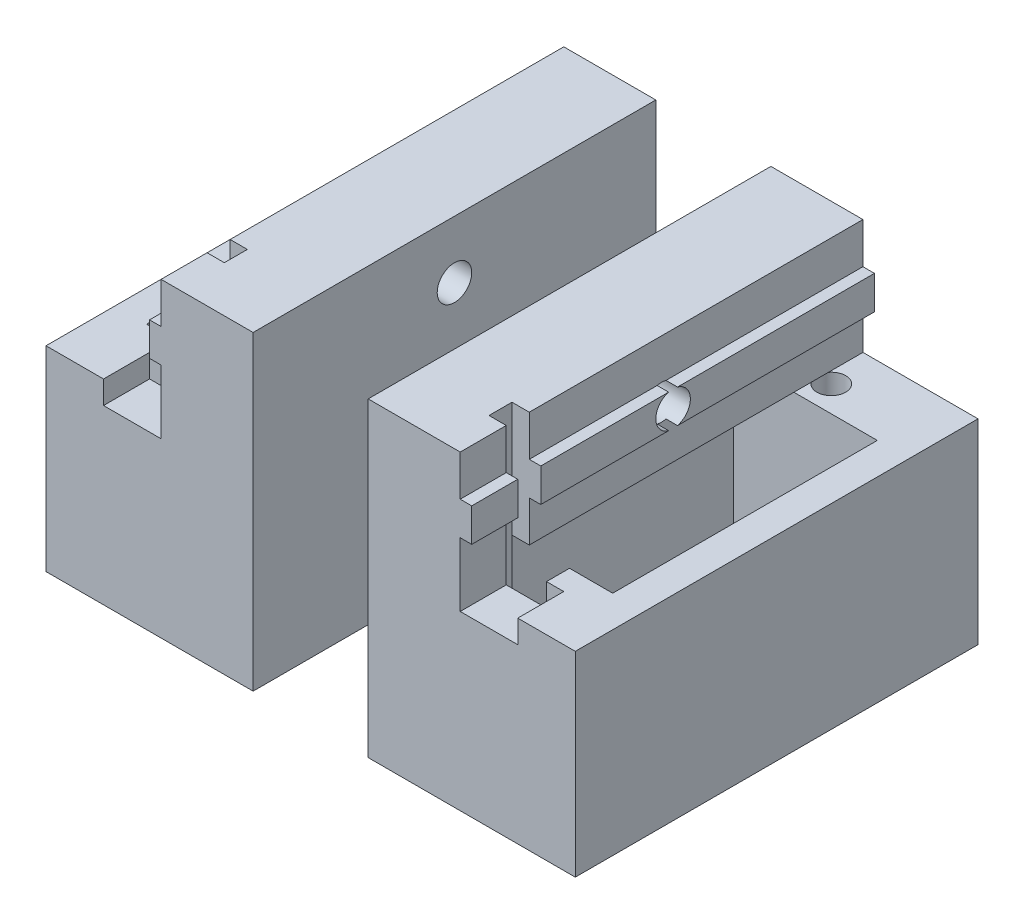
SolidWorks part; units mm, degrees
ref_plane "Front Plane" through (0, 0, 0) normal (0, 0, 1) x (1, 0, 0)
ref_plane "Top Plane" through (0, 0, 0) normal (0, 1, 0) x (1, 0, 0)
ref_plane "Right Plane" through (0, 0, 0) normal (1, 0, 0) x (0, 0, -1)
sketch "Sketch1" plane through (0, 0, 0) normal (0, 0, 1) x (1, 0, 0)
  line L0 (9, 0) -> (9, 17)
  line L1 (9, 17) -> (-9, 17)
  line L2 (-9, 17) -> (-9, 0)
  line L3 (-9, 0) -> (9, 0)
  point P11 (0, 0)
  dimension "D1" = 18
  dimension "D3" = 17
extrude "Main" add sketch "Sketch1" along normal mid plane 35
sketch "Sketch2" plane through (0, 17, 0) normal (0, 1, 0) x (1, 0, 0)
  circle A1 centre (0, 13.75) radius 1.25
  dimension "D1" = 13.75
  dimension "D3" = 2.5
extrude "FixingHole" cut sketch "Sketch2" against normal through all
sketch "Sketch3" plane through (0, 17, 0) normal (0, 1, 0) x (1, 0, 0)
  line L0 (-9, -17.5) -> (-9, 17.5) construction
  line L1 (-6.25, 11.5) -> (6.25, 11.5)
  line L2 (-6.25, 11.5) -> (-6.25, -11.5)
  line L3 (-6.25, -11.5) -> (-2.5, -11.5)
  line L4 (6.25, 11.5) -> (6.25, -11.5)
  line L5 (9, -17.5) -> (9, 17.5) construction
  line L6 (-2.5, -11.5) -> (-2.5, -13.5)
  line L7 (-2.5, -13.5) -> (2.5, -13.5)
  line L8 (2.5, -13.5) -> (2.5, -11.5)
  line L9 (2.5, -11.5) -> (6.25, -11.5)
  point P6 (6.25, 0)
  dimension "D1" = 23
  dimension "D2" = 12.5
  dimension "D3" = 2.75
  dimension "D4" = 2.75
  dimension "D5" = 5
  dimension "D6" = 2
extrude "ServoSquareHole" cut sketch "Sketch3" against normal through all
sketch "Sketch4" plane through (0, 0, 17.5) normal (0, 0, 1) x (1, 0, 0)
  line L0 (9, 17) -> (9, 27)
  line L2 (9, 27) -> (1, 27)
  line L3 (1, 27) -> (1, 23.45)
  line L4 (1, 23.45) -> (0, 23.45)
  line L5 (0, 23.45) -> (0, 20.55)
  line L6 (0, 20.55) -> (1, 20.55)
  line L7 (1, 20.55) -> (1, 17)
  line L8 (9, 17) -> (-9, 17) construction
  line L9 (1, 17) -> (9, 17)
  line L10 (-9, 17) -> (-9, 0) construction
  dimension "D1" = 2.9
  dimension "D2" = 10
  dimension "D3" = 1
  dimension "D4" = 10
  dimension "D5" = 8
extrude "Boss-Extrude1" add sketch "Sketch4" against normal up to surface (35 mm away) up to face at (0, 8.5, -17.5)
sketch "Sketch5" plane through (9, 0, 0) normal (1, 0, 0) x (0, 0, -1)
  line L0 (17.5, 27) -> (-17.5, 27) construction
  circle A0 centre (0, 22) radius 1.5
  dimension "D1" = 3
  dimension "D2" = 5
extrude "Cut-Extrude1" cut sketch "Sketch5" against normal through all
sketch "Sketch6" plane through (0, 0, 0) normal (0, -1, 0) x (-1, 0, 0)
  line L1 (2.5, -13.5) -> (-2.5, -13.5)
  line L2 (2.5, -13.5) -> (2.5, -11.5)
  line L3 (2.5, -11.5) -> (-2.5, -11.5)
  line L4 (-2.5, -13.5) -> (-2.5, -11.5)
extrude "Cut-Extrude2" cut sketch "Sketch6" against normal through all
sketch "Sketch7" plane through (0, 0, 17.5) normal (0, 0, 1) x (1, 0, 0)
  line L1 (1, 17) -> (-4, 17)
  line L2 (1, 17) -> (1, 15)
  line L3 (1, 15) -> (-4, 15)
  line L4 (-4, 17) -> (-4, 15)
  dimension "D1" = 5
  dimension "D2" = 2
extrude "Cut-Extrude3" cut sketch "Sketch7" against normal up to surface (4 mm away) up to face at (0.4, 17.6, 13.5)
ref_plane "Plane1" through (14, 0, 0) normal (1, 0, 0) x (0, 0, -1)
mirror "Mirror1" about plane through (14, 0, 0) normal (1, 0, 0) of bodies 108
